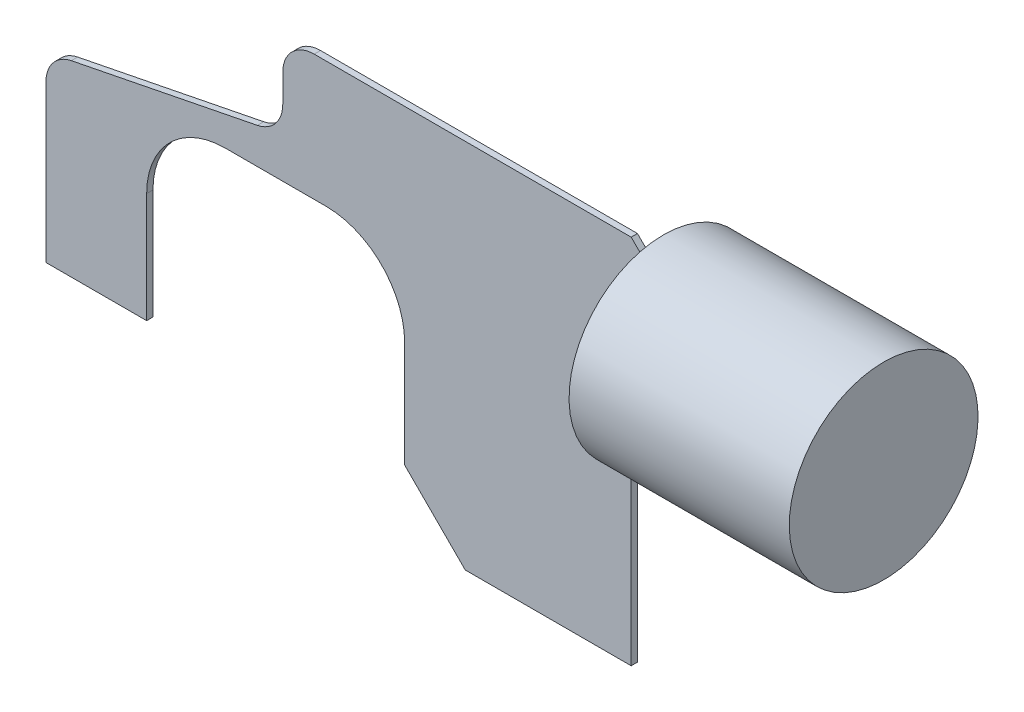
SolidWorks part; units mm, degrees
material "Nickel"
ref_plane "Front Plane" through (0, 0, 0) normal (0, 0, 1) x (1, 0, 0)
ref_plane "Top Plane" through (0, 0, 0) normal (0, 1, 0) x (1, 0, 0)
ref_plane "Right Plane" through (0, 0, 0) normal (1, 0, 0) x (0, 0, -1)
sketch "Sketch1" plane through (0, 0, 0) normal (0, 0, 1) x (1, 0, 0)
  line L0 (0, 0) -> (0, 9.525)
  line L1 (3.175, 12.7) -> (23.622, 12.7)
  line L2 (23.622, 12.7) -> (24.797, 11.525)
  line L3 (24.797, 11.525) -> (24.797, 7.525)
  line L4 (24.797, 7.525) -> (23.622, 6.35)
  line L5 (23.622, 6.35) -> (23.622, -2.286)
  line L6 (23.622, -2.286) -> (16.9237, -2.286)
  line L7 (16.9237, -2.286) -> (14.478, 0.1597)
  line L8 (14.478, 0.1597) -> (14.478, 4.445)
  line L9 (11.303, 7.62) -> (7.239, 7.62)
  line L10 (4.064, 4.445) -> (4.064, 0)
  line L11 (4.064, 0) -> (0, 0)
  arc A0 (0, 9.525) -> (3.175, 12.7) centre (3.175, 9.525) cw
  arc A1 (14.478, 4.445) -> (11.303, 7.62) centre (11.303, 4.445) ccw
  arc A2 (7.239, 7.62) -> (4.064, 4.445) centre (7.239, 4.445) ccw
  point P15 (0, 12.7)
  dimension "D4" = 3.175
  dimension "D5" = 3.175
  dimension "D1" = 12.7
  dimension "D2" = 14.986
  dimension "D3" = 5.08
  dimension "D6" = 45
  dimension "D7" = 9.144
  dimension "D8" = 23.622
  dimension "D9" = 4.064
extrude "Boss-Extrude1" add sketch "Sketch1" against normal mid plane 0.254
sketch "Sketch5" plane through (24.797, 0, 0) normal (1, 0, 0) x (0, 0, -1)
  line L0 (0.127, 11.525) -> (-0.127, 11.525) construction
  circle A0 centre (0, 9.493) radius 3.81
  point P4 (0, 11.525)
  dimension "D2" = 7.62
  dimension "D1" = 2.032
extrude "Boss-Extrude2" add sketch "Sketch5" along normal blind 8.89
sketch "Sketch6" plane through (0, 0, 0.127) normal (0, 0, 1) x (1, 0, 0)
  line L0 (4.826, 10.922) -> (4.826, 8.382)
  line L1 (4.826, 8.382) -> (9.144, 9.652)
  line L2 (9.144, 9.652) -> (4.826, 10.922)
  line L3 (0, 9.525) -> (0, 0) construction
  line L4 (23.622, 12.7) -> (3.175, 12.7) construction
  point P6 (4.826, 9.652)
  dimension "D1" = 9.144
  dimension "D2" = 2.54
  dimension "D3" = 4.318
  dimension "D4" = 1.778
extrude "Cut-Extrude1" cut sketch "Sketch6" against normal through all
sketch "Sketch8" plane through (0, 0, -0.127) normal (0, 0, -1) x (-1, 0, 0)
  line L0 (-9.557, 11.43) -> (-9.557, 10.3088)
  line L1 (-23.622, 12.7) -> (-3.175, 12.7) construction
  line L2 (-8.5347, 9.0632) -> (-1.0223, 7.5693)
  line L3 (0, 9.525) -> (0, 0) construction
  line L4 (-24.797, 7.525) -> (-24.797, 11.525) construction
  line L5 (-10.827, 12.7) -> (-21.5655, 12.7)
  line L6 (-21.5655, 12.7) -> (-4.064, 0)
  line L7 (-4.064, 0) -> (0, 0)
  line L8 (0, 0) -> (0, 6.3237)
  line L9 (-10.827, 12.7) -> (0, 12.7)
  line L10 (0, 12.7) -> (0, 6.3237)
  arc A0 (0, 6.3237) -> (-1.0223, 7.5693) centre (-1.27, 6.3237) ccw
  arc A1 (-8.5347, 9.0632) -> (-9.557, 10.3088) centre (-8.287, 10.3088) cw
  arc A2 (-9.557, 11.43) -> (-10.827, 12.7) centre (-10.827, 11.43) ccw
  point P16 (0, 7.366)
  point P21 (-9.557, 12.7)
  line M1 (-9.144, 9.652) -> (-4.826, 10.922)
  line M2 (-4.826, 10.922) -> (-4.826, 8.382)
  line M3 (-4.826, 8.382) -> (-9.144, 9.652)
  line M5 (0, 0) -> (0, 9.525)
  arc M6 (0, 9.525) -> (-3.175, 12.7) centre (-3.175, 9.525) ccw
  line M7 (-3.175, 12.7) -> (-23.622, 12.7)
  dimension "D3" = 1.27
  dimension "D1" = 15.24
  dimension "D2" = 7.366
extrude "Cut-Extrude3" cut sketch "Sketch8" against normal blind 2.54 contours A2 L0 A1 L2 A0 M5 M6 M7 M3 M1 M2
